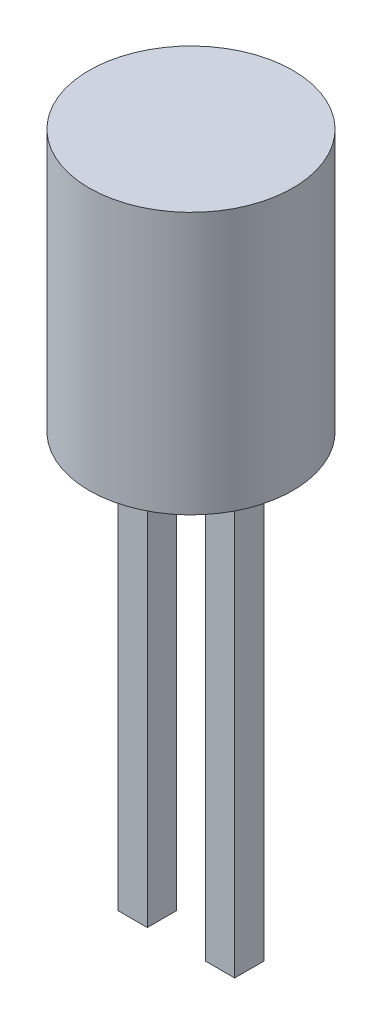
SolidWorks part; units mm, degrees
ref_plane "Front Plane" through (0, 0, 0) normal (0, 0, 1) x (1, 0, 0)
ref_plane "Top Plane" through (0, 0, 0) normal (0, 1, 0) x (1, 0, 0)
ref_plane "Right Plane" through (0, 0, 0) normal (1, 0, 0) x (0, 0, -1)
sketch "Sketch1" plane through (0, 0, 0) normal (0, 1, 0) x (1, 0, 0)
  circle A0 centre (0, 0) radius 3.5
  dimension "D1" = 7
extrude "Boss-Extrude1" add sketch "Sketch1" along normal blind 9
sketch "Sketch2" plane through (0, 9, 0) normal (0, 1, 0) x (1, 0, 0)
  line L1 (-2, 0.5) -> (-1, 0.5)
  line L2 (-2, 0.5) -> (-2, -0.5)
  line L3 (-2, -0.5) -> (-1, -0.5)
  line L4 (-1, 0.5) -> (-1, -0.5)
  line L5 (1, 0.5) -> (2, 0.5)
  line L6 (1, 0.5) -> (1, -0.5)
  line L7 (1, -0.5) -> (2, -0.5)
  line L8 (2, 0.5) -> (2, -0.5)
  dimension "D1" = 1
  dimension "D2" = 1
  dimension "D3" = 1
  dimension "D4" = 1
  dimension "D5" = 2
  dimension "D6" = 1
  dimension "D7" = 0.5
  dimension "D8" = 0.5
extrude "Boss-Extrude2" add sketch "Sketch2" against normal blind 24
equation "\"0.5mm.\"=0.574247"
